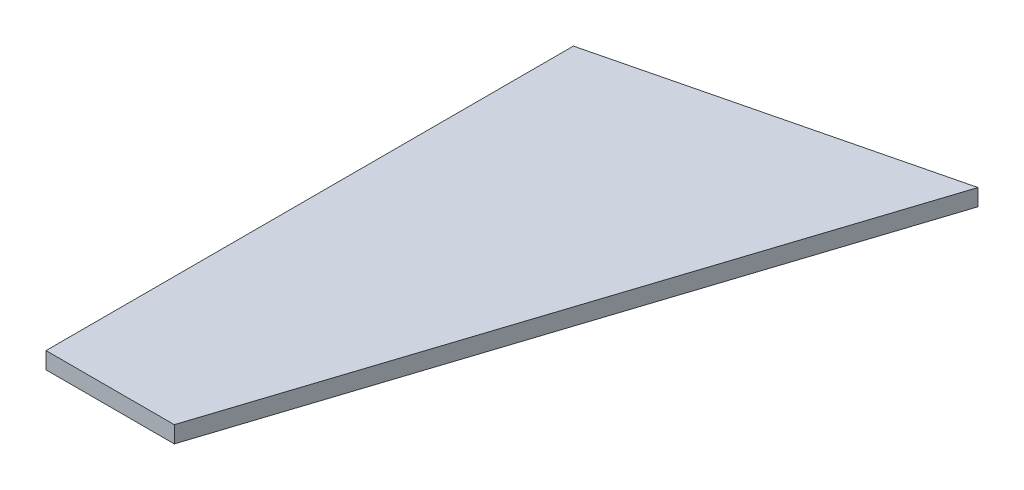
SolidWorks part; units mm, degrees
ref_plane "Plan de face" through (0, 0, 0) normal (0, 0, 1) x (1, 0, 0)
ref_plane "Plan de dessus" through (0, 0, 0) normal (0, 1, 0) x (1, 0, 0)
ref_plane "Plan de droite" through (0, 0, 0) normal (1, 0, 0) x (0, 0, -1)
sketch "Esquisse1" plane through (0, 0, 0) normal (0, 1, 0) x (1, 0, 0)
  line L1 (38.904, 72.7353) -> (0, 63.1769)
  line L2 (0, 63.1769) -> (0, 0)
  line L3 (0, 0) -> (15.3697, 0)
  line L5 (38.904, 72.7353) -> (15.3697, 0)
extrude "Boss.-Extru.1" add sketch "Esquisse1" along normal blind 2
